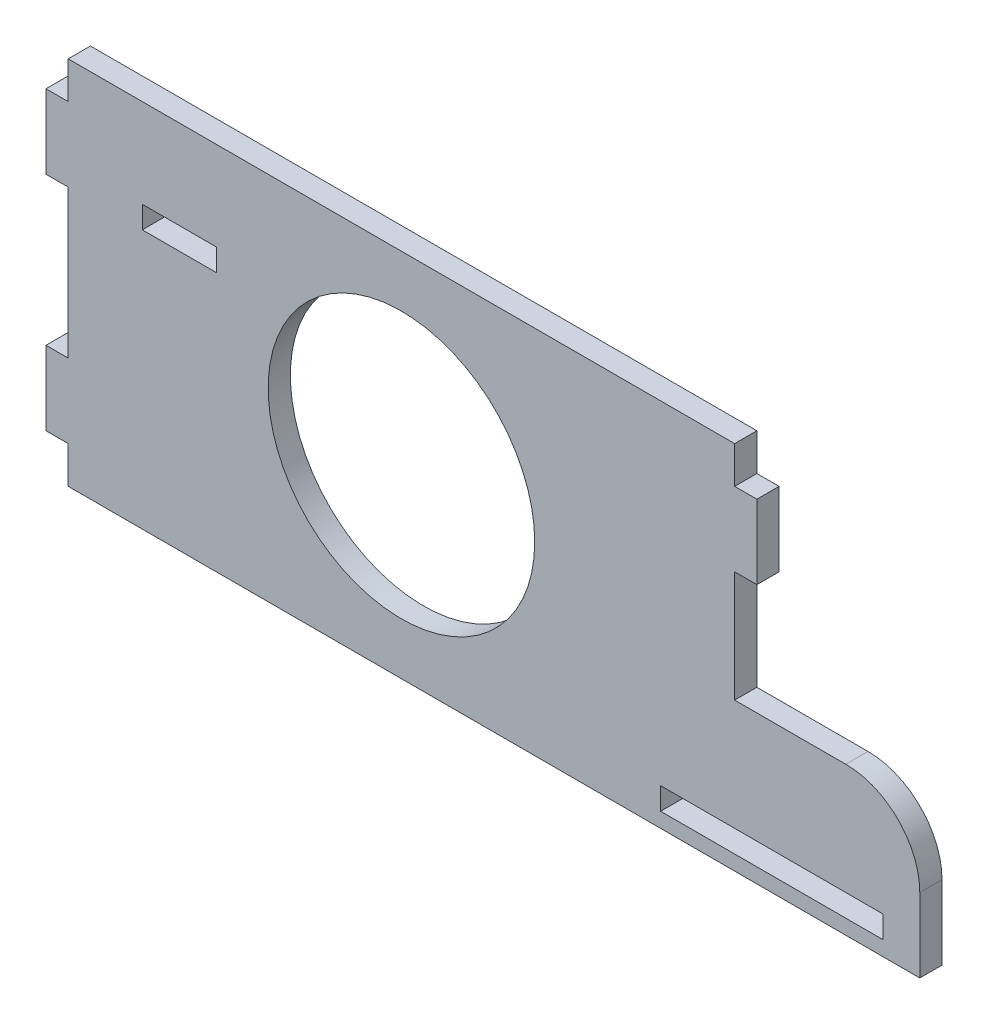
SolidWorks part; units mm, degrees
ref_plane "Front Plane" through (0, 0, 0) normal (0, 0, 1) x (1, 0, 0)
ref_plane "Top Plane" through (0, 0, 0) normal (0, 1, 0) x (1, 0, 0)
ref_plane "Right Plane" through (0, 0, 0) normal (1, 0, 0) x (0, 0, -1)
sketch "Sketch1" plane through (0, 0, 0) normal (0, 0, 1) x (1, 0, 0)
  line L0 (-45, 10) -> (-45, -10)
  line L1 (45, 25) -> (-45, 25)
  line L2 (45, 25) -> (45, 20)
  line L4 (-45, 25) -> (-45, 20)
  line L5 (-45, -20) -> (-45, -25)
  line L7 (-48, 20) -> (-45, 20)
  line L8 (-48, 20) -> (-48, 10)
  line L9 (-48, 10) -> (-45, 10)
  line L10 (48, 20) -> (48, 10)
  line L11 (-45, -25) -> (70, -25)
  line L13 (-48, -10) -> (-45, -10)
  line L14 (-48, -10) -> (-48, -20)
  line L15 (-48, -20) -> (-45, -20)
  line L17 (-35, 13) -> (-25, 13)
  line L18 (35, -23) -> (65, -23)
  line L19 (45, -5) -> (60, -5)
  line L22 (70, -15) -> (70, -25)
  line L23 (35, -23) -> (35, -20)
  line L24 (35, -20) -> (65, -20)
  line L25 (65, -23) -> (65, -20)
  line L26 (-35, 13) -> (-35, 10)
  line L27 (-35, 10) -> (-25, 10)
  line L28 (45, 20) -> (48, 20)
  line L29 (-25, 13) -> (-25, 10)
  line L30 (-35, 13) -> (-25, 10) construction
  line L31 (-35, 10) -> (-25, 13) construction
  line L32 (45, 10) -> (48, 10)
  line L35 (45, 10) -> (45, -5)
  circle A0 centre (0, 0) radius 18
  arc A1 (60, -5) -> (70, -15) centre (60, -15) cw
  point P17 (70, -5)
  point P21 (-30, 11.5)
  point P30 (0, 0)
  dimension "D3" = 30
  dimension "D7" = 10
  dimension "D1" = 90
  dimension "D2" = 50
  dimension "D4" = 3
  dimension "D5" = 20
  dimension "D6" = 25
  dimension "D8" = 20
extrude "Boss-Extrude1" add sketch "Sketch1" along normal blind 3
